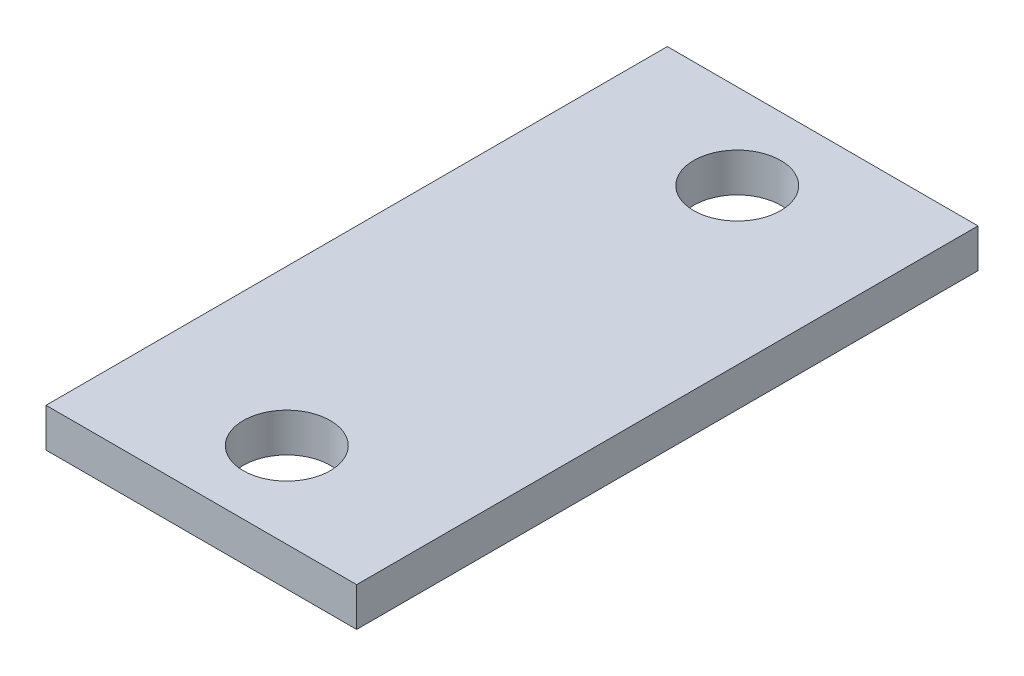
SolidWorks part; units mm, degrees
material "Plain Carbon Steel"
ref_plane "Front Plane" through (0, 0, 0) normal (0, 0, 1) x (1, 0, 0)
ref_plane "Top Plane" through (0, 0, 0) normal (0, 1, 0) x (1, 0, 0)
ref_plane "Right Plane" through (0, 0, 0) normal (1, 0, 0) x (0, 0, -1)
sketch "Sketch1" plane through (0, 0, 0) normal (0, 1, 0) x (1, 0, 0)
  line L1 (0, 0) -> (50.8, 0)
  line L2 (0, 0) -> (0, 101.6)
  line L3 (0, 101.6) -> (50.8, 101.6)
  line L4 (50.8, 0) -> (50.8, 101.6)
  line L8 (0, 13.97) -> (50.8, 13.97) construction
  circle A0 centre (25.4, 13.97) radius 7.112
  circle A1 centre (25.4, 87.63) radius 7.112
  dimension "D6" = 14.224
  dimension "D1" = 101.6
  dimension "D2" = 87.63
  dimension "D3" = 25.4
  dimension "D5" = 50.8
  dimension "D7" = 87.63
extrude "Hammer" add sketch "Sketch1" along normal blind 6.35
